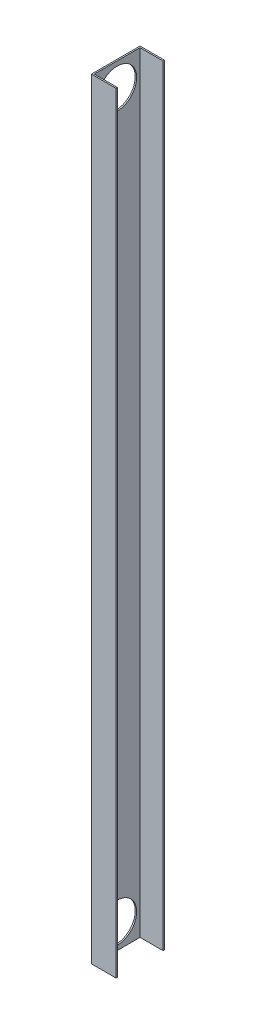
SolidWorks part; units mm, degrees
ref_plane "Front Plane" through (0, 0, 0) normal (0, 0, 1) x (1, 0, 0)
ref_plane "Top Plane" through (0, 0, 0) normal (0, 1, 0) x (1, 0, 0)
ref_plane "Right Plane" through (0, 0, 0) normal (1, 0, 0) x (0, 0, -1)
sketch "Sketch2" plane through (0, 0, 0) normal (0, 1, 0) x (1, 0, 0)
  line L0 (-22.5, 47.5) -> (25.5, 47.5)
  line L1 (-25.5, 50.5) -> (25.5, 50.5)
  line L2 (-25.5, 50.5) -> (-25.5, -50.5)
  line L3 (-25.5, -50.5) -> (25.5, -50.5)
  line L4 (25.5, 50.5) -> (25.5, 47.5)
  line L6 (-22.5, -47.5) -> (25.5, -47.5)
  line L7 (-22.5, 47.5) -> (-22.5, -47.5)
  line L8 (22.5, 47.5) -> (22.5, -47.5) construction
  line L9 (-22.5, 47.5) -> (22.5, 47.5) construction
  line L10 (-22.5, -47.5) -> (22.5, -47.5) construction
  line L11 (25.5, -47.5) -> (25.5, -50.5)
  line L13 (25.5, 50.5) -> (25.5, -50.5) construction
  point P4 (-25.5, 0)
  point P6 (0, 50.5)
  dimension "D1" = 101
  dimension "D2" = 51
  dimension "D3" = 3
extrude "Boss-Extrude2" add sketch "Sketch2" along normal blind 1600
sketch "Sketch3" plane through (-25.5, 0, 0) normal (-1, 0, 0) x (0, 0, 1)
  circle A0 centre (0, 50) radius 40.5
  circle A1 centre (0, 1550) radius 40.5
  dimension "D1" = 81
  dimension "D3" = 81
  dimension "D2" = 50
  dimension "D4" = 1500
extrude "Cut-Extrude2" cut sketch "Sketch3" against normal through all contours A0
